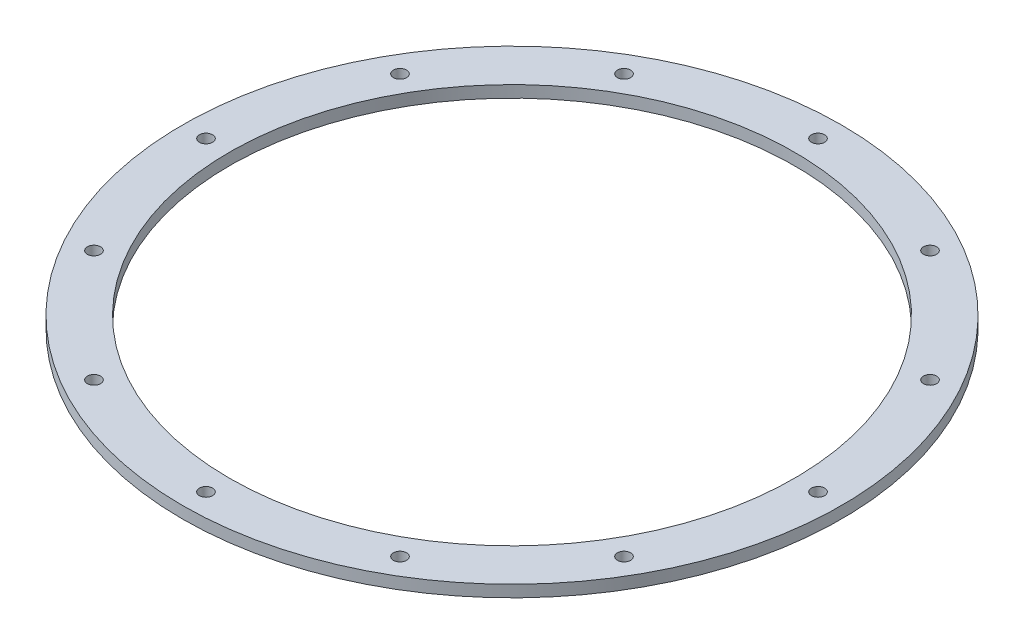
SolidWorks part; units mm, degrees
material "PTFE (general)"
ref_plane "Front Plane" through (0, 0, 0) normal (0, 0, 1) x (1, 0, 0)
ref_plane "Top Plane" through (0, 0, 0) normal (0, 1, 0) x (1, 0, 0)
ref_plane "Right Plane" through (0, 0, 0) normal (1, 0, 0) x (0, 0, -1)
ref_axis "Axis1" through (0, 55, 0) along (0, -1, 0)
sketch "Sketch1" plane through (0, 0, 0) normal (0, 0, 1) x (1, 0, 0)
  line L0 (-38.1, 0) -> (0, 0) construction
  line L1 (-38.1, 0) -> (-44.45, 0)
  line L2 (-38.1, 0) -> (-38.1, 1.5875)
  line L3 (-38.1, 1.5875) -> (-44.45, 1.5875)
  line L4 (-44.45, 0) -> (-44.45, 1.5875)
  line L7 (0, 1.5875) -> (-38.1, 1.5875) construction
  point P12 (-44.45, 0)
  point P18 (-38.1, 1.5875)
revolve "Main" add sketch "Sketch1" angle 360 about axis through (0, 55, 0) along (0, -1, 0)
sketch "Hole Location" plane through (0, 0, 0) normal (0, 1, 0) x (1, 0, 0)
  line L0 (0, 0) -> (-41.275, 0) construction
  circle A0 centre (0, 0) radius 41.275 construction
  dimension "D1" = 82.55
hole_wizard "#50 (0.07) Diameter Hole1" positions "Sketch3" profile "Sketch5" hole size "#50" standard "ANSI Inch" end condition through all
sketch "Sketch3" plane through (0, 0, 0) normal (0, -1, 0) x (-1, 0, 0)
  point P0 (41.275, 0)
sketch "Sketch5" plane through (-41.275, 0, 0) normal (1, 0, 0) x (0, 0, -1)
  line L0 (0, 0) -> (0, 1.5875)
  line L1 (0, 1.5875) -> (0.889, 1.5875)
  line L2 (0.889, 1.5875) -> (0.889, 0)
  line L5 (0.889, 0) -> (0, 0)
  line L11 (0, -6.35) -> (0, 107.95) construction
  dimension "Thru Hole Dia." = 1.778
  dimension "Thru Hole Depth" = 1.5875
pattern_circular "Screw Passthroughs" count 12 over 360 about axis through (0, 0, 0) along (0, 1, 0) of "#50 (0.07) Diameter Hole1"
equation "\"D1@Hole Location\"=\"TANK DIAMETER@Cryo Tank.Assembly\"+\"GASKET SEAT THICKNESS@Cryo Tank.Assembly\""
